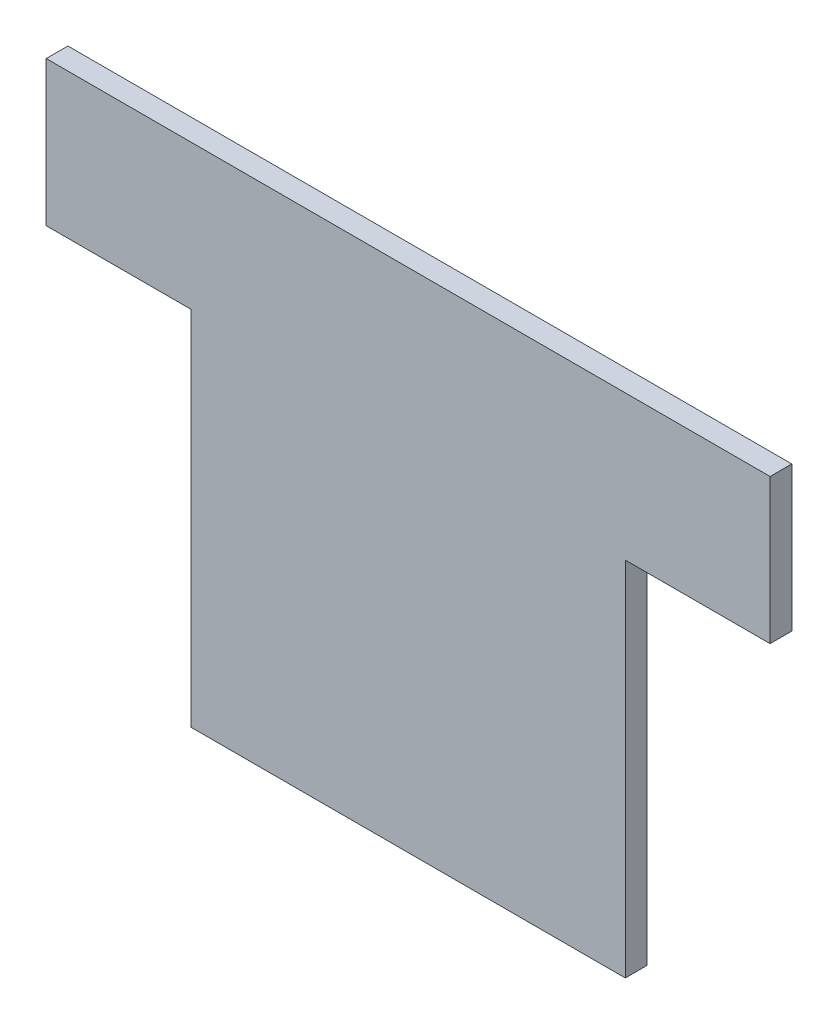
SolidWorks part; units mm, degrees
ref_plane "Front Plane" through (0, 0, 0) normal (0, 0, 1) x (1, 0, 0)
ref_plane "Top Plane" through (0, 0, 0) normal (0, 1, 0) x (1, 0, 0)
ref_plane "Right Plane" through (0, 0, 0) normal (1, 0, 0) x (0, 0, -1)
sketch "Sketch1" plane through (0, 0, 0) normal (0, 0, 1) x (1, 0, 0)
  line L0 (-30, -20) -> (-30, -70)
  line L1 (-30, -70) -> (30, -70)
  line L2 (30, -70) -> (30, -20)
  line L3 (30, -20) -> (50, -20)
  line L4 (50, -20) -> (50, 0)
  line L5 (50, 0) -> (-50, 0)
  line L6 (-50, 0) -> (-50, -20)
  line L7 (-50, -20) -> (-30, -20)
  point P8 (0, 0)
  dimension "D1" = 60
  dimension "D2" = 20
  dimension "D3" = 20
  dimension "D4" = 50
extrude "Boss-Extrude1" add sketch "Sketch1" along normal blind 3
